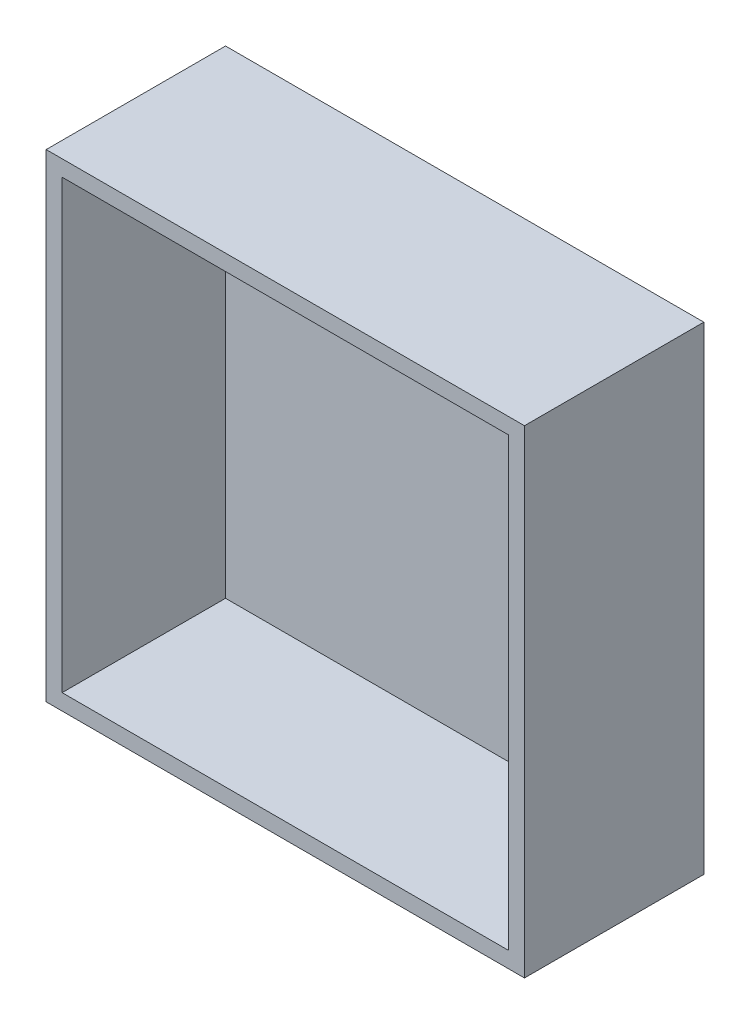
SolidWorks part; units mm, degrees
ref_plane "Спереди" through (0, 0, 0) normal (0, 0, 1) x (1, 0, 0)
ref_plane "Сверху" through (0, 0, 0) normal (0, 1, 0) x (1, 0, 0)
ref_plane "Справа" through (0, 0, 0) normal (1, 0, 0) x (0, 0, -1)
other "Configuration Table"
sketch "Эскиз1" plane through (0, 0, 0) normal (0, 0, 1) x (1, 0, 0)
  line L1 (-30, -30) -> (30, -30)
  line L2 (-30, -30) -> (-30, 30)
  line L3 (-30, 30) -> (30, 30)
  line L4 (30, -30) -> (30, 30)
  line L5 (0, 30) -> (0, -30) construction
  line L6 (-30, 0) -> (30, 0) construction
  point P0 (0, 0)
  dimension "D1" = 60
  dimension "D2" = 60
extrude "основа" add sketch "Эскиз1" along normal blind 22.5
sketch "Эскиз2" plane through (0, 0, 22.5) normal (0, 0, 1) x (1, 0, 0)
  line L0 (0, 30) -> (0, -30) construction
  line L1 (30, 30) -> (-30, 30) construction
  line L2 (-30, -30) -> (30, -30) construction
  line L3 (-30, 0) -> (30, 0) construction
  line L4 (-30, 30) -> (-30, -30) construction
  line L5 (30, -30) -> (30, 30) construction
  line L7 (-28, -28) -> (28, -28)
  line L8 (-28, -28) -> (-28, 28)
  line L9 (-28, 28) -> (28, 28)
  line L10 (28, -28) -> (28, 28)
  line L11 (0, 28) -> (0, -28) construction
  line L12 (-28, 0) -> (28, 0) construction
  point P12 (0, 0)
  dimension "D1" = 56
  dimension "D2" = 56
extrude "Вырез-Вытянуть1" cut sketch "Эскиз2" against normal blind 20.5
sketch "Эскиз4" plane through (0, 0, 2) normal (0, 0, 1) x (1, 0, 0)
  line L0 (0, 28) -> (0, -28) construction
  line L1 (28, 28) -> (-28, 28) construction
  line L2 (-28, -28) -> (28, -28) construction
  line L3 (-28, 0) -> (28, 0) construction
  line L4 (-28, 28) -> (-28, -28) construction
  line L5 (28, -28) -> (28, 28) construction
  line L6 (28, 0) -> (-28, 0) construction
  line L7 (-23, 28) -> (-23, 21.2194) construction
  line L8 (28, 28) -> (-28, 28) construction
  line L9 (-28, 23.5) -> (-18, 23.5) construction
  line L10 (-28, 28) -> (-28, -28) construction
  line L12 (-28, 28) -> (-18, 28)
  line L13 (-28, 28) -> (-28, 19)
  line L14 (-28, 19) -> (-18, 19)
  line L15 (-18, 28) -> (-18, 19)
  line L16 (-23, 19) -> (-23, 28) construction
  line L17 (-28, 23.5) -> (-18, 23.5) construction
  point P20 (-23, 23.5)
  dimension "D1" = 23
  dimension "D2" = 23.5
  dimension "D3" = 0
  dimension "D4" = 0
extrude "Бобышка-Вытянуть2" add sketch "Эскиз4" along normal blind 9
sketch "Эскиз5" plane through (0, 0, 11) normal (0, 0, 1) x (1, 0, 0)
  line L0 (-23, 28) -> (-23, 19) construction
  line L1 (-18, 28) -> (-28, 28) construction
  line L2 (-28, 19) -> (-18, 19) construction
  line L3 (-28, 23.5) -> (-18, 23.5) construction
  line L4 (-28, 28) -> (-28, 19) construction
  line L5 (-18, 19) -> (-18, 28) construction
  circle A0 centre (-23, 23.5) radius 1
  dimension "D1" = 2
extrude "Вырез-Вытянуть2" cut sketch "Эскиз5" against normal blind 8.8
